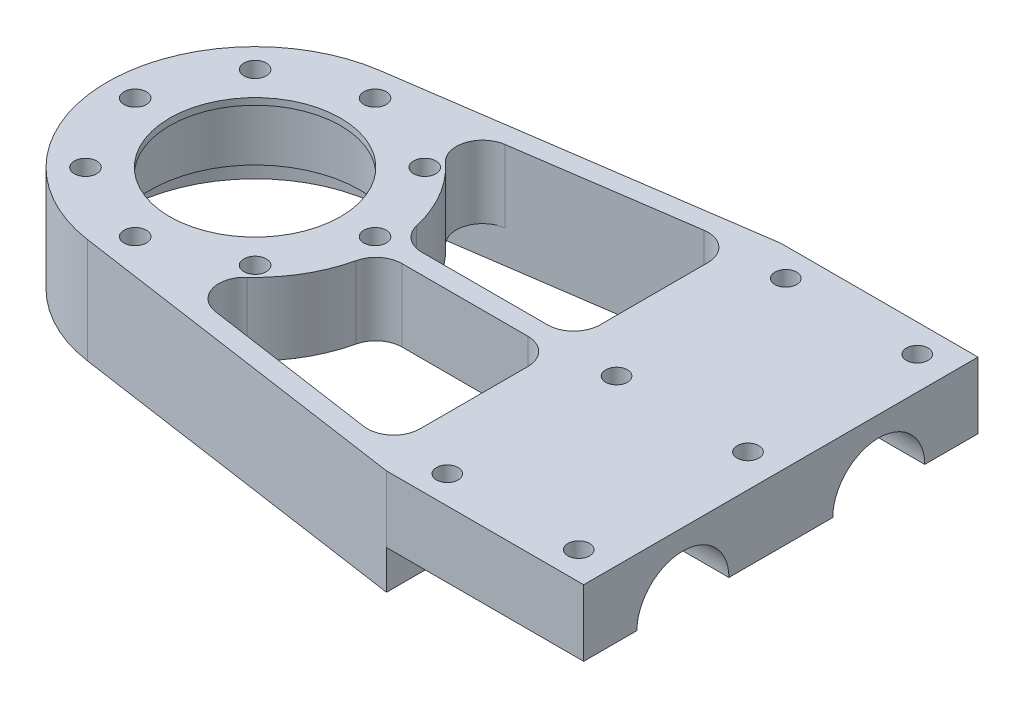
SolidWorks part; units mm, degrees
material "3.1355 (EN-AW 2024)"
ref_plane "Front" through (0, 0, 0) normal (0, 0, 1) x (1, 0, 0)
ref_plane "Top" through (0, 0, 0) normal (0, 1, 0) x (1, 0, 0)
ref_plane "Right" through (0, 0, 0) normal (1, 0, 0) x (0, 0, -1)
sketch "Эскиз1" plane through (0, 0, 0) normal (0, 1, 0) x (1, 0, 0)
  line L0 (0, 0) -> (0, 60)
  line L1 (0, 60) -> (-30, 60)
  line L2 (0, 30) -> (-130, 30) construction
  line L3 (-30, 60) -> (-30, 30) construction
  line L4 (-30, 60) -> (-83.2348, 52.2663)
  line L5 (-30, 0) -> (-83.2348, 7.7337)
  line L6 (0, 0) -> (-30, 0)
  circle A0 centre (-80, 30) radius 22.5 construction
  arc A1 (-83.2348, 52.2663) -> (-83.2348, 7.7337) centre (-80, 30) ccw
  dimension "D2" = 45
  dimension "D1" = 60
  dimension "D3" = 30
  dimension "D4" = 130
  dimension "D5" = 50
extrude "Бобышка-Вытянуть1" add sketch "Эскиз1" along normal blind 16
sketch "Эскиз2" plane through (0, 0, 0) normal (0, -1, 0) x (1, 0, 0)
  circle A0 centre (-80, -30) radius 16
  dimension "D1" = 32
extrude "Вырез-Вытянуть1" cut sketch "Эскиз2" against normal offset from surface (15 mm away) 1 up to face at (-40.9558, 16, -30)
sketch "Эскиз3" plane through (0, 15, 0) normal (0, -1, 0) x (1, 0, 0)
  circle A0 centre (-80, -30) radius 13
  dimension "D1" = 26
extrude "Вырез-Вытянуть2" cut sketch "Эскиз3" against normal through all
sketch "Эскиз4" plane through (0, 0, 0) normal (0, -1, 0) x (1, 0, 0)
  circle A0 centre (-80, -30) radius 20.5
  dimension "D1" = 41
extrude "Вырез-Вытянуть3" cut sketch "Эскиз4" against normal offset from surface (5 mm away) 10 up to face at (-80, 15, -43)
sketch "Эскиз5" plane through (0, 5, 0) normal (0, -1, 0) x (1, 0, 0)
  line L0 (-80, -30) -> (-98.25, -30) construction
  line L1 (-80, -30) -> (-92.9047, -17.0953) construction
  line L2 (-80, -30) -> (-67.0953, -17.0953) construction
  line L3 (-80, -30) -> (-67.0953, -42.9047) construction
  line L4 (-80, -30) -> (-92.9047, -42.9047) construction
  line L5 (-80, -30) -> (-80, -11.75) construction
  line L6 (-80, -30) -> (-61.75, -30) construction
  line L7 (-80, -30) -> (-80, -48.25) construction
  circle A0 centre (-80, -30) radius 18.25 construction
  circle A1 centre (-80, -30) radius 20.5 construction
  point P13 (-80, -30)
  point P17 (-80, -30)
  dimension "D1" = 36.5
  dimension "D2" = 45
  dimension "D3" = 4
  dimension "D4" = 4
hole_wizard "Отверстие с зазором M32" positions "Эскиз19" profile "Эскиз18" hole size "M3" standard "Ansi Metric" end condition through all
sketch "Эскиз19" plane through (0, 5, 0) normal (0, -1, 0) x (-1, 0, 0)
  point P0 (92.9047, 17.0953)
  point P3 (67.0953, 17.0953)
  point P6 (67.0953, 42.9047)
  point P9 (92.9047, 42.9047)
  point P12 (80, 11.75)
  point P15 (61.75, 30)
  point P18 (80, 48.25)
  point P21 (98.25, 30)
sketch "Эскиз18" plane through (-92.9047, 5, -17.0953) normal (1, 0, 0) x (0, 0, -1)
  line L0 (0, 0) -> (0, 11)
  line L1 (0, 11) -> (1.7, 11)
  line L2 (1.7, 11) -> (1.7, 0)
  line L5 (1.7, 0) -> (0, 0)
  line L11 (0, -6.35) -> (0, 107.95) construction
  dimension "Диаметр сквозного отверстия" = 3.4
  dimension "Глубина сквозного отверстия" = 11
sketch "Эскиз8" plane through (0, 0, 0) normal (1, 0, 0) x (0, 0, -1)
  line L0 (30, 16) -> (30, 0) construction
  line L1 (8.1, 5.9) -> (0, 5.9)
  line L2 (0, 16) -> (60, 16) construction
  line L3 (51.9, 5.9) -> (60, 5.9)
  line L4 (22.1, 5.9) -> (37.9, 5.9)
  line L5 (52.5, 0) -> (7.5, 0) construction
  line L6 (0, 16) -> (0, 0) construction
  line L7 (48.667, 0) -> (60, 0)
  line L8 (18.867, 0) -> (41.133, 0)
  line L18 (0, 0) -> (60, 0)
  line L19 (60, 0) -> (60, 16)
  line L20 (60, 16) -> (0, 16)
  line L21 (0, 16) -> (0, 0)
  line L22 (0, 0) -> (11.333, 0)
  line L23 (60, 0) -> (60, 5.9)
  line L25 (0, 5.9) -> (0, 0)
  circle A0 centre (15.1, 5.9) radius 7
  circle A1 centre (44.9, 5.9) radius 7
  line M3 (0, 0) -> (60, 0)
  line M4 (60, 0) -> (60, 16)
  line M6 (0, 16) -> (0, 0)
  dimension "D1" = 14
  dimension "D3" = 10.1
  dimension "D4" = 0
  dimension "D2" = 15.1
extrude "Вырез-Вытянуть8" cut sketch "Эскиз8" against normal blind 30 contours A0 M3 | A0 L1 M6 M3 | L4 L0 L8 A1 | A1 M3 | L3 A1 M3 M4 | L0 L4 A0 M3
sketch "Эскиз12" plane through (0, 0, 0) normal (0, -1, 0) x (1, 0, 0)
  line L0 (-30, 0) -> (-83.2348, -7.7337) construction
  line L1 (-30, -60) -> (-83.2348, -52.2663) construction
  line L2 (-30, -60) -> (-30, -30) construction
  line L3 (-30, 0) -> (-76.5229, -6.7587)
  line L4 (-30, -60) -> (-76.5229, -53.2413)
  line L5 (-30, -60) -> (-30, 0)
  circle A2 centre (-80, -30) radius 23.5
  arc A3 (-76.5229, -53.2413) -> (-76.5229, -6.7587) centre (-80, -30) ccw
  dimension "D1" = 3
extrude "Вырез-Вытянуть9" [suppressed] cut sketch "Эскиз12" against normal up to surface (5.9 mm away)
sketch "Эскиз13" [suppressed] plane through (0, 3.1366, 0) normal (0, -1, 0) x (1, 0, 0)
  line L4 (-27, -24.6401) -> (-27, -35.3599)
  line L5 (-27, -24.6401) -> (-27, -35.3599)
  line L26 (-3, -35.3599) -> (-3, -24.6401)
  line L27 (-3, -24.6401) -> (-27, -24.6401)
  line L36 (-27, -35.3599) -> (-3, -35.3599)
  arc A0 (-76.5229, -53.2413) -> (-76.5229, -6.7587) centre (-80, -30) ccw construction
  arc A1 (-69.8248, -51.1829) -> (-69.8248, -8.8171) centre (-80, -30) ccw
  dimension "D1" = 3
extrude "Вырез-Вытянуть10" [suppressed] cut sketch "Эскиз13" against normal through all
sketch "Эскиз14" plane through (0, 0, 0) normal (0, -1, 0) x (1, 0, 0)
  line L9 (-33, -56.5327) -> (-82.8035, -49.2974)
  line L10 (-33, -3.4673) -> (-33, -56.5327)
  line L11 (-82.8035, -10.7026) -> (-33, -3.4673)
  line L12 (-33, -56.5327) -> (-76.5446, -50.2067)
  line L13 (-33, -3.4673) -> (-33, -56.5327)
  line L14 (-76.5446, -9.7933) -> (-33, -3.4673)
  circle A0 centre (-80, -30) radius 20.5 construction
  arc A1 (-76.5446, -50.2067) -> (-76.5446, -9.7933) centre (-80, -30) ccw
  dimension "D1" = 3
extrude "Вырез-Вытянуть11" cut sketch "Эскиз14" against normal through all
sketch "Эскиз15" plane through (0, 5, 0) normal (0, -1, 0) x (1, 0, 0)
  line L0 (-59.5, -30) -> (-33, -30) construction
  line L1 (-33, -56.5327) -> (-33, -3.4673) construction
  line L2 (-59.555, -31.5) -> (-33, -31.5)
  line L3 (-59.555, -28.5) -> (-33, -28.5)
  line L4 (-59.5, -28.5) -> (-33, -28.5) construction
  line L5 (-59.5, -31.5) -> (-33, -31.5) construction
  line L6 (-33, -28.5) -> (-33, -31.5)
  arc A0 (-76.5446, -50.2067) -> (-76.5446, -9.7933) centre (-80, -30) ccw construction
  arc A1 (-59.555, -31.5) -> (-59.555, -28.5) centre (-80, -30) ccw
  dimension "D1" = 1.5
  dimension "D2" = 1.5
extrude "Бобышка-Вытянуть2" add sketch "Эскиз15" against normal through all
fillet "Скругление1" radius 4 8 edges at (-33, 8, -3.4673) (-76.5446, 10.5, -9.7933) (-33, 10.5, -28.5) (-59.555, 10.5, -28.5) (-33, 8, -56.5327) (-33, 10.5, -31.5) (-59.555, 10.5, -31.5) (-76.5446, 10.5, -50.2067)
hole_wizard "Отверстие обработанное метчиком M4x0.71" positions "Эскиз23" profile "Эскиз24" tap size "M4x0.7" standard "Ansi Metric" end condition through all
sketch "Эскиз23" plane through (-72.5396, 5.9, -28.0043) normal (0, -1, 0) x (-0.7071, 0, 0.7071)
  point P0 (-67.3769, -28.1386)
  point P3 (-53.2348, -13.9964)
  point P6 (-35.0268, -32.2044)
  point P9 (-49.1689, -46.3466)
  point P12 (-30.9609, -64.5546)
  point P15 (-16.8188, -50.4124)
sketch "Эскиз24" plane through (-5, 5.9, -55.75) normal (1, 0, 0) x (0, 0, -1)
  line L0 (0, 0) -> (0, 10.1)
  line L1 (0, 10.1) -> (1.65, 10.1)
  line L2 (1.65, 10.1) -> (1.65, 0)
  line L3 (1.65, 0) -> (0, 0)
  line L4 (0, -6.35) -> (0, 107.95) construction
  dimension "Диаметр проходного сверла" = 3.3
  dimension "Глубина проходного сверла" = 10.1
cosmetic thread "Отверстие резьбы11" parameters "D2"=4
cosmetic thread "Отверстие резьбы12" parameters "D2"=4
cosmetic thread "Отверстие резьбы13" parameters "D2"=4
cosmetic thread "Отверстие резьбы14" parameters "D2"=4
cosmetic thread "Отверстие резьбы15" parameters "D2"=4
cosmetic thread "Отверстие резьбы16" parameters "D2"=4
equation "\"D4@Эскиз1\"=\"D3@Эскиз1\"+100"
equation "\"D1@Эскиз5\"=32+4.5"
